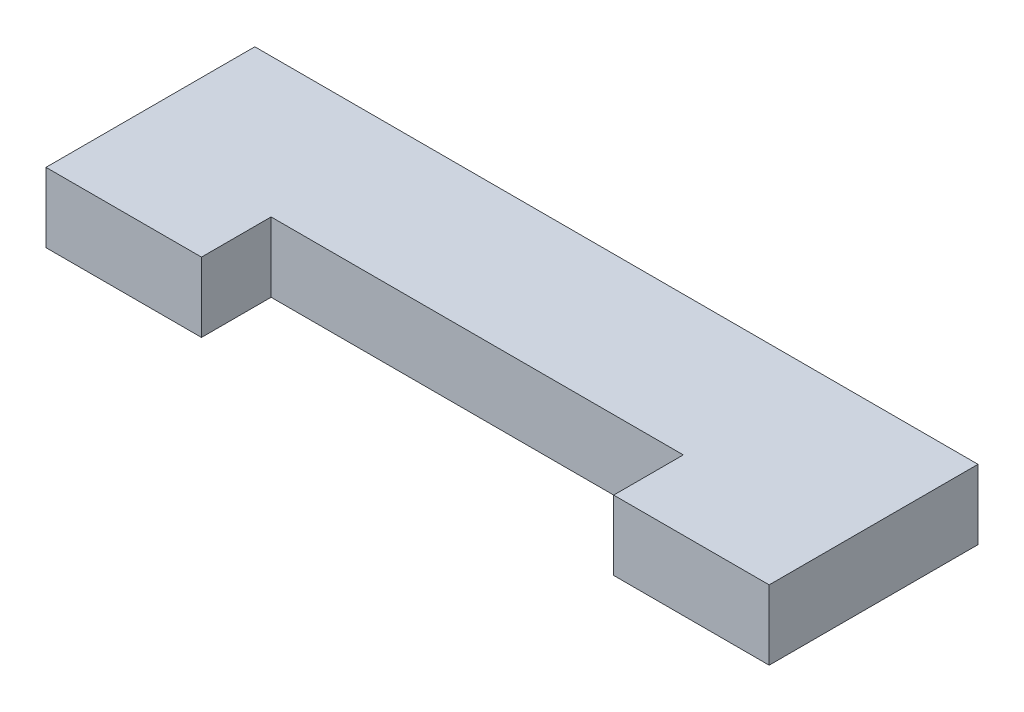
SolidWorks part; units mm, degrees
ref_plane "Front Plane" through (0, 0, 0) normal (0, 0, 1) x (1, 0, 0)
ref_plane "Top Plane" through (0, 0, 0) normal (0, 1, 0) x (1, 0, 0)
ref_plane "Right Plane" through (0, 0, 0) normal (1, 0, 0) x (0, 0, -1)
sketch "Sketch1" plane through (0, 0, 0) normal (0, 1, 0) x (1, 0, 0)
  line L0 (-20, -3.85) -> (-20, -7.7)
  line L1 (-11.4, -3.85) -> (11.4, -3.85)
  line L2 (-20, -3.85) -> (-20, 3.85)
  line L3 (-20, 3.85) -> (20, 3.85)
  line L4 (20, -3.85) -> (20, 3.85)
  line L5 (-20, -3.85) -> (20, 3.85) construction
  line L6 (-20, 3.85) -> (20, -3.85) construction
  line L7 (-20, -7.7) -> (-11.4, -7.7)
  line L8 (-11.4, -7.7) -> (-11.4, -3.85)
  line L9 (0, -55) -> (0, 55) construction
  line L10 (11.4, -7.7) -> (11.4, -3.85)
  line L11 (20, -7.7) -> (11.4, -7.7)
  line L12 (20, -3.85) -> (20, -7.7)
  line L13 (11.4, -3.85) -> (20, -3.85) construction
  line L14 (-20, -3.85) -> (-11.4, -3.85) construction
  point P0 (0, 0)
  dimension "D1" = 7.7
  dimension "D2" = 40
  dimension "D3" = 3.85
  dimension "D4" = 8.6
extrude "Boss-Extrude1" add sketch "Sketch1" along normal blind 3.85
equation "\"m3_hole\"= 3.5"
equation "\"m3_washer\"= 7.3"
equation "\"m3_nut\"= 5.3"
equation "\"plywood_thickness\" = 3.85"
equation "\"guide_width\"= 10.0"
equation "\"guide_length\"= 65.0"
equation "\"guide_tab_length\" = 10.0"
equation "\"guide_tab_width\" = 9.0"
equation "\"guide_thickness\" = 12.0"
equation "\"grinder_od\"= 52.0"
equation "\"grinder_id\"= 45.5"
equation "\"grinder_adjust_od\" = 58.0"
equation "\"funnel_width_from_adjust_ring\" = 13.0"
equation "\"drill_contact_diameter_small\" = 24.0"
equation "\"drill_contact_diameter_medium\" = 28.0"
equation "\"drill_contact_diameter_large\" = 39.0"
equation "\"drill_contact_diameter_tab\" = 31.0"
equation "\"drill_contact_ow_tab\" = 14.5"
equation "\"drill_contact_iw_tab\" = 8.7"
equation "\"drill_contact_small_height\" = 15.5"
equation "\"drill_contact_large_height\" = 34.5"
equation "\"plywood_peg_length\" = 40"
equation "\"plywood_peg_width\" = 8.3"
equation "\"D1@Sketch1\"=\"plywood_thickness\"*2"
equation "\"D2@Sketch1\"=\"plywood_peg_length\""
equation "\"D3@Sketch1\"=\"plywood_thickness\""
equation "\"D4@Sketch1\"=\"plywood_peg_width\"+0.3"
equation "\"D1@Boss-Extrude1\"=\"plywood_thickness\""
